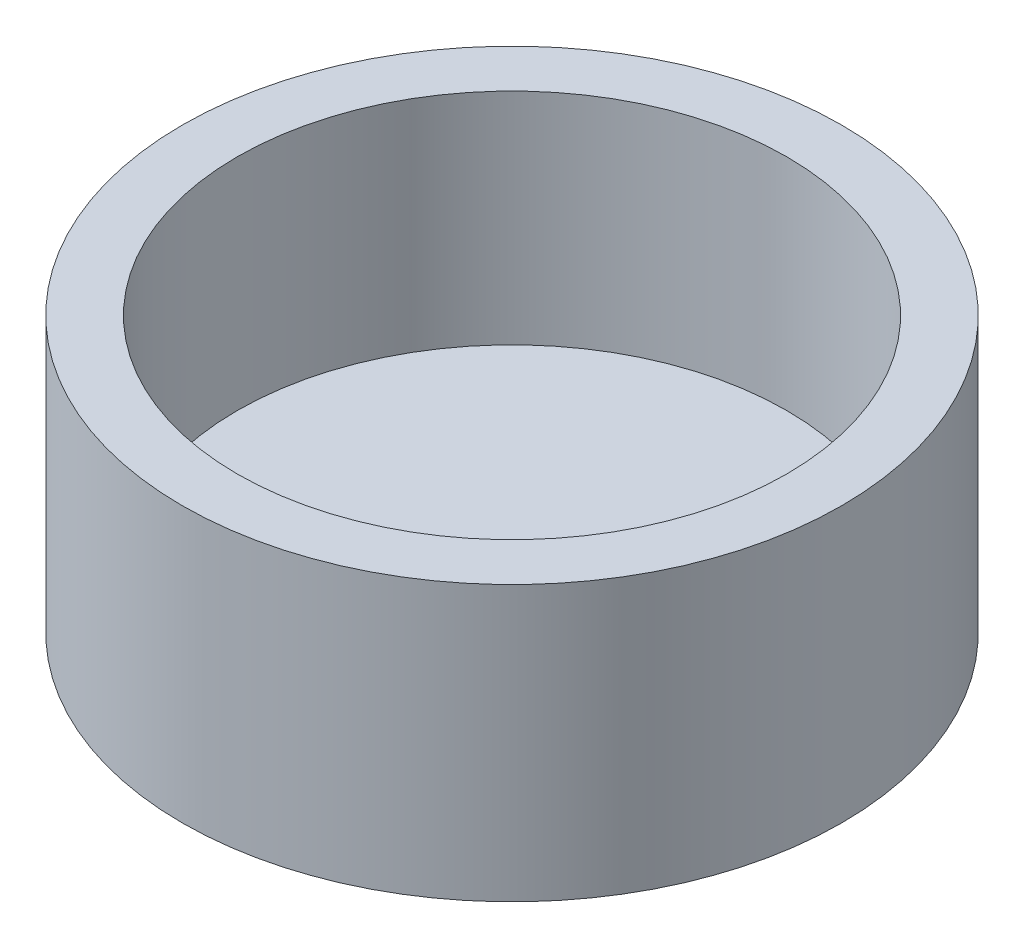
SolidWorks part; units mm, degrees
ref_plane "Front Plane" through (0, 0, 0) normal (0, 0, 1) x (1, 0, 0)
ref_plane "Top Plane" through (0, 0, 0) normal (0, 1, 0) x (1, 0, 0)
ref_plane "Right Plane" through (0, 0, 0) normal (1, 0, 0) x (0, 0, -1)
sketch "Sketch1" plane through (0, 0, 0) normal (0, 1, 0) x (1, 0, 0)
  circle A0 centre (-5.4251, 4.3107) radius 15
  dimension "D1" = 30
extrude "Boss-Extrude1" add sketch "Sketch1" along normal blind 12.5
sketch "Sketch2" plane through (0, 12.5, 0) normal (0, 1, 0) x (1, 0, 0)
  circle A0 centre (-5.4251, 4.3107) radius 12.5
  circle A1 centre (-5.4251, 4.3107) radius 15 construction
  dimension "D1" = 25
extrude "Cut-Extrude1" cut sketch "Sketch2" against normal blind 10
